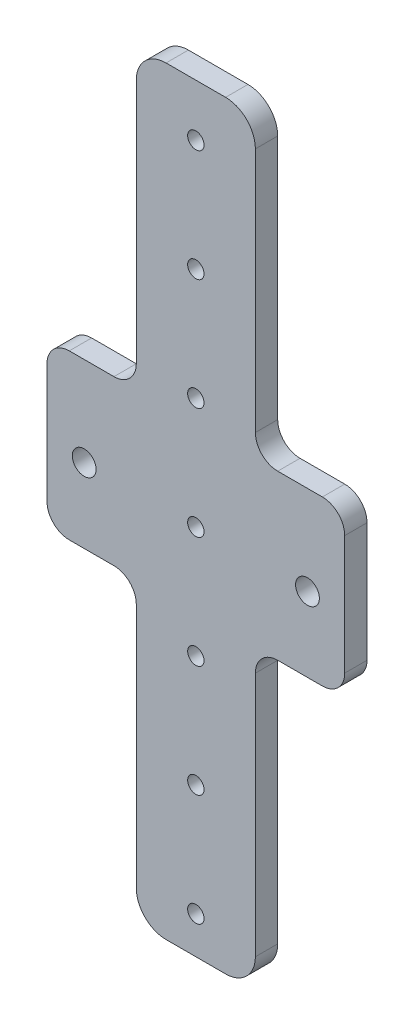
SolidWorks part; units mm, degrees
material "A-玻璃纤维"
ref_plane "前视基准面" through (0, 0, 0) normal (0, 0, 1) x (1, 0, 0)
ref_plane "上视基准面" through (0, 0, 0) normal (0, 1, 0) x (1, 0, 0)
ref_plane "右视基准面" through (0, 0, 0) normal (1, 0, 0) x (0, 0, -1)
sketch "草图1" plane through (0, 0, 0) normal (0, 0, 1) x (1, 0, 0)
  line L0 (0, 82.1094) -> (0, -82.7796) construction
  line L1 (-113.054, 0) -> (117.0757, 0) construction
  line L3 (-20, -75) -> (20, -75)
  line L4 (-20, -75) -> (-20, 75)
  line L5 (-20, 75) -> (20, 75)
  line L6 (20, -75) -> (20, 75)
  line L7 (-20, -75) -> (20, 75) construction
  line L8 (-20, 75) -> (20, -75) construction
  circle A0 centre (-15, 0) radius 1.6
  circle A1 centre (15, 0) radius 1.6
  point P5 (0, 0)
  dimension "D1" = 30
  dimension "D2" = 3.2
  dimension "D3" = 150
  dimension "D4" = 40
extrude "凸台-拉伸1" add sketch "草图1" along normal blind 3
sketch "草图2" plane through (0, 0, 3) normal (0, 0, 1) x (1, 0, 0)
  line L0 (0, 93.8705) -> (0, -98.3772) construction
  circle A0 centre (0, 0) radius 1.1
  circle A1 centre (0, 15) radius 1.1
  circle A2 centre (0, 30) radius 1.1
  circle A3 centre (0, 45) radius 1.1
  circle A4 centre (0, 60) radius 1.1
  circle A5 centre (0, 0) radius 1.1
  circle A6 centre (0, 15) radius 1.1
  circle A7 centre (0, 30) radius 1.1
  circle A8 centre (0, 45) radius 1.1
  circle A9 centre (0, -15) radius 1.1
  circle A10 centre (0, 0) radius 1.1
  circle A11 centre (0, 15) radius 1.1
  circle A12 centre (0, 30) radius 1.1
  circle A13 centre (0, -30) radius 1.1
  circle A14 centre (0, -15) radius 1.1
  circle A15 centre (0, 0) radius 1.1
  circle A16 centre (0, 15) radius 1.1
  circle A17 centre (0, -45) radius 1.1
  circle A18 centre (0, -30) radius 1.1
  circle A19 centre (0, -15) radius 1.1
  circle A20 centre (0, 0) radius 1.1
  circle A21 centre (0, -15) radius 1.1
  circle A22 centre (0, -30) radius 1.1
  circle A23 centre (0, -45) radius 1.1
  circle A24 centre (0, -60) radius 1.1
  dimension "D1" = 2.2
  dimension "D4" = 15
  dimension "D2" = 5
  dimension "D3" = 5
extrude "切除-拉伸1" cut sketch "草图2" against normal through all contours A24 L0 | L0 A24 | A23 L0 | L0 A17 | A22 L0 | L0 A13 | L0 A0 | A20 L0 | A16 L0 | A21 L0 | L0 A9 | A1 | A2 | A3 | A4
sketch "草图4" plane through (0, 0, 3) normal (0, 0, 1) x (1, 0, 0)
  line L0 (-20, -57) -> (20, -57)
  line L1 (-20, 75) -> (-20, -75) construction
  line L2 (20, -75) -> (20, 75) construction
  line L3 (20, -57) -> (20, -75)
  line L4 (-20, -75) -> (20, -75) construction
  line L5 (20, -75) -> (-20, -75)
  line L6 (-20, -75) -> (-20, -57)
  dimension "D1" = 18
extrude "切除-拉伸3" cut sketch "草图4" against normal blind 10
sketch "草图5" plane through (0, 0, 3) normal (0, 0, 1) x (1, 0, 0)
  line L0 (-20, 75) -> (20, 75)
  line L1 (20, 75) -> (20, 87)
  line L2 (20, 87) -> (-20, 87)
  line L3 (-20, 87) -> (-20, 75)
  dimension "D1" = 12
extrude "凸台-拉伸2" add sketch "草图5" against normal up to surface (3 mm away) up to face at (0, 9, 0)
sketch "草图6" plane through (0, 0, 3) normal (0, 0, 1) x (1, 0, 0)
  line L0 (0, -73.1082) -> (0, 136.2333) construction
  circle A0 centre (0, 75) radius 1.1
  circle A2 centre (0, 60) radius 1.1 construction
  dimension "D1" = 15
extrude "切除-拉伸4" cut sketch "草图6" against normal blind 10
sketch "草图7" plane through (0, 0, 3) normal (0, 0, 1) x (1, 0, 0)
  line L0 (-20, 12) -> (-8, 12)
  line L1 (-20, 87) -> (-20, -57) construction
  line L2 (-8, 12) -> (-8, 87)
  line L3 (20, 87) -> (-20, 87) construction
  line L4 (-8, 87) -> (-20, 87)
  line L5 (-20, 87) -> (-20, 12)
  line L6 (0, 110.4736) -> (0, -93.0103) construction
  line L7 (-20, -10) -> (-8, -10)
  line L8 (-8, -10) -> (-8, -57)
  line L9 (20, -57) -> (-20, -57) construction
  line L10 (-8, -57) -> (-20, -57)
  line L11 (-20, -57) -> (-20, -10)
  line L12 (20, -57) -> (20, -10)
  line L13 (8, -57) -> (20, -57)
  line L14 (8, -10) -> (8, -57)
  line L15 (20, -10) -> (8, -10)
  line L16 (20, 87) -> (20, 12)
  line L17 (8, 87) -> (20, 87)
  line L18 (8, 12) -> (8, 87)
  line L19 (20, 12) -> (8, 12)
  circle A0 centre (-15, 0) radius 1.6 construction
  dimension "D1" = 10
  dimension "D2" = 12
  dimension "D3" = 12
extrude "切除-拉伸5" cut sketch "草图7" against normal blind 10
fillet "圆角1" radius 3 12 edges at (-8, -57, 1.5) (8, -57, 1.5) (8, -10, 1.5) (20, -10, 1.5) (20, 12, 1.5) (8, 12, 1.5) (8, 87, 1.5) (-8, 87, 1.5) (-8, 12, 1.5) (-20, 12, 1.5) (-20, -10, 1.5) (-8, -10, 1.5)
sketch "草图8" plane through (0, 0, 3) normal (0, 0, 1) x (1, 0, 0)
  line L0 (8, 52) -> (-8, 52)
  line L3 (8, -50) -> (-8, -50)
  line L6 (-8, 52) -> (-8, 94.1392)
  line L7 (-8, 94.1392) -> (8, 94.1392)
  line L8 (8, 94.1392) -> (8, 52)
  line L9 (-8, -50) -> (-8, -71.4179)
  line L10 (-8, -71.4179) -> (8, -71.4179)
  line L11 (8, -71.4179) -> (8, -50)
  line L12 (8, 84) -> (8, 15) construction
  line L13 (-8, 15) -> (-8, 84) construction
  line L14 (-8, -54) -> (-8, -13) construction
  line L15 (8, -13) -> (8, -54) construction
  circle A0 centre (0, 0) radius 1.1 construction
  circle A1 centre (0, -45) radius 1.1 construction
  dimension "D1" = 52
  dimension "D2" = 5
extrude "切除-拉伸6" cut sketch "草图8" against normal blind 10
fillet "圆角2" radius 4 4 edges at (-8, -50, 1.5) (8, -50, 1.5) (8, 52, 1.5) (-8, 52, 1.5)
